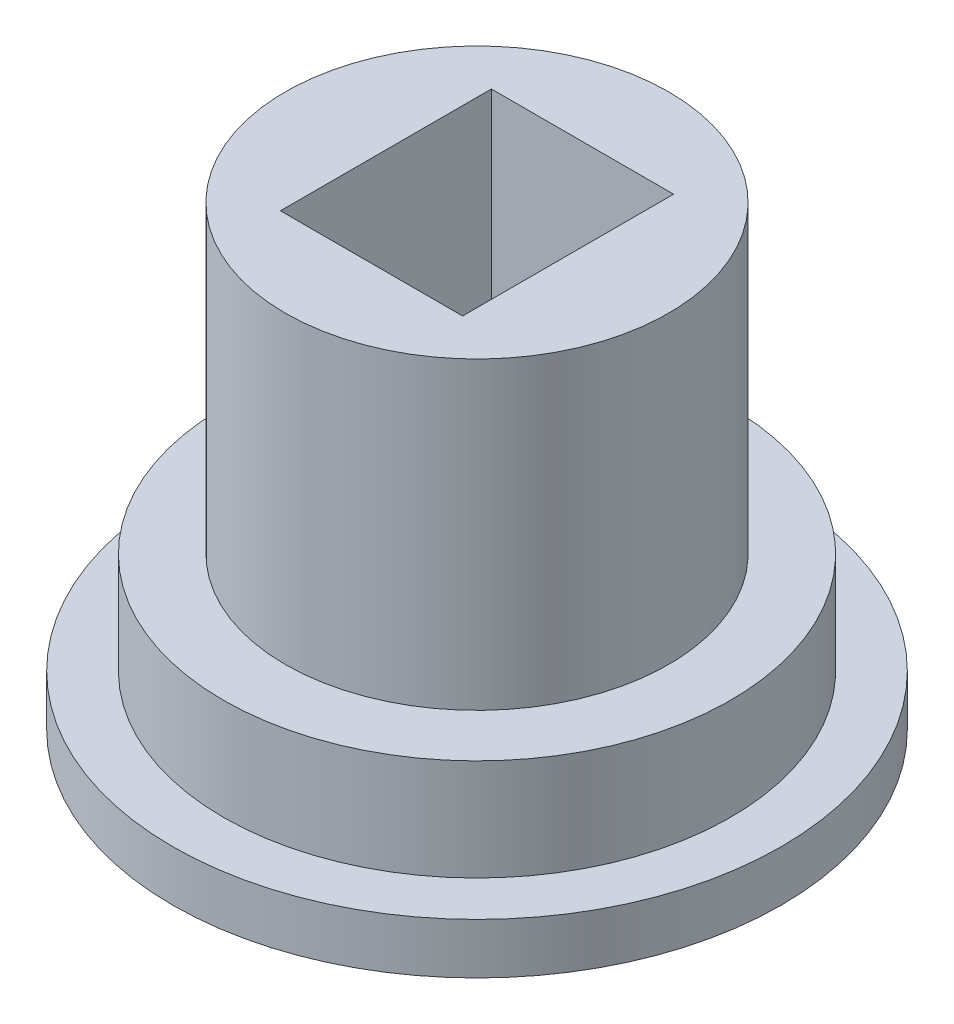
SolidWorks part; units mm, degrees
ref_plane "Front Plane" through (0, 0, 0) normal (0, 0, 1) x (1, 0, 0)
ref_plane "Top Plane" through (0, 0, 0) normal (0, 1, 0) x (1, 0, 0)
ref_plane "Right Plane" through (0, 0, 0) normal (1, 0, 0) x (0, 0, -1)
sketch "Sketch1" plane through (0, 0, 0) normal (0, 1, 0) x (1, 0, 0)
  circle A0 centre (0, 0) radius 6.35
extrude "Boss-Extrude1" add sketch "Sketch1" along normal blind 2.54
sketch "Sketch2" plane through (0, 2.54, 0) normal (0, 1, 0) x (1, 0, 0)
  circle A0 centre (0, 0) radius 4.8006
extrude "Boss-Extrude2" add sketch "Sketch2" along normal blind 7.62
sketch "Sketch3" plane through (0, 10.16, 0) normal (0, 1, 0) x (1, 0, 0)
  line L1 (-2.2814, -2.6416) -> (2.2814, -2.6416)
  line L2 (-2.2814, -2.6416) -> (-2.2814, 2.6416)
  line L3 (-2.2814, 2.6416) -> (2.2814, 2.6416)
  line L4 (2.2814, -2.6416) -> (2.2814, 2.6416)
  line L5 (-2.2814, -2.6416) -> (2.2814, 2.6416) construction
  line L6 (-2.2814, 2.6416) -> (2.2814, -2.6416) construction
  point P0 (0, 0)
  dimension "D1" = 0
extrude "Cut-Extrude1" cut sketch "Sketch3" against normal blind 7.62
sketch "Sketch6" plane through (0, 0, 0) normal (0, -1, 0) x (1, 0, 0)
  circle A0 centre (0, 0) radius 7.62
extrude "Boss-Extrude3" add sketch "Sketch6" along normal blind 1.27
sketch "Sketch4" plane through (0, 2.54, 0) normal (0, 1, 0) x (1, 0, 0)
  circle A0 centre (0, -1.27) radius 0.762
  point P0 (0, 0)
  point P1 (0, -1.27)
  dimension "D1" = 1.27
sketch "Sketch5" plane through (0, 2.54, 0) normal (0, 1, 0) x (1, 0, 0)
  circle A0 centre (0, 1.27) radius 0.762
  point P0 (0, 1.27)
extrude "Cut-Extrude2" cut sketch "Sketch4" against normal through all
extrude "Cut-Extrude3" cut sketch "Sketch5" against normal through all
